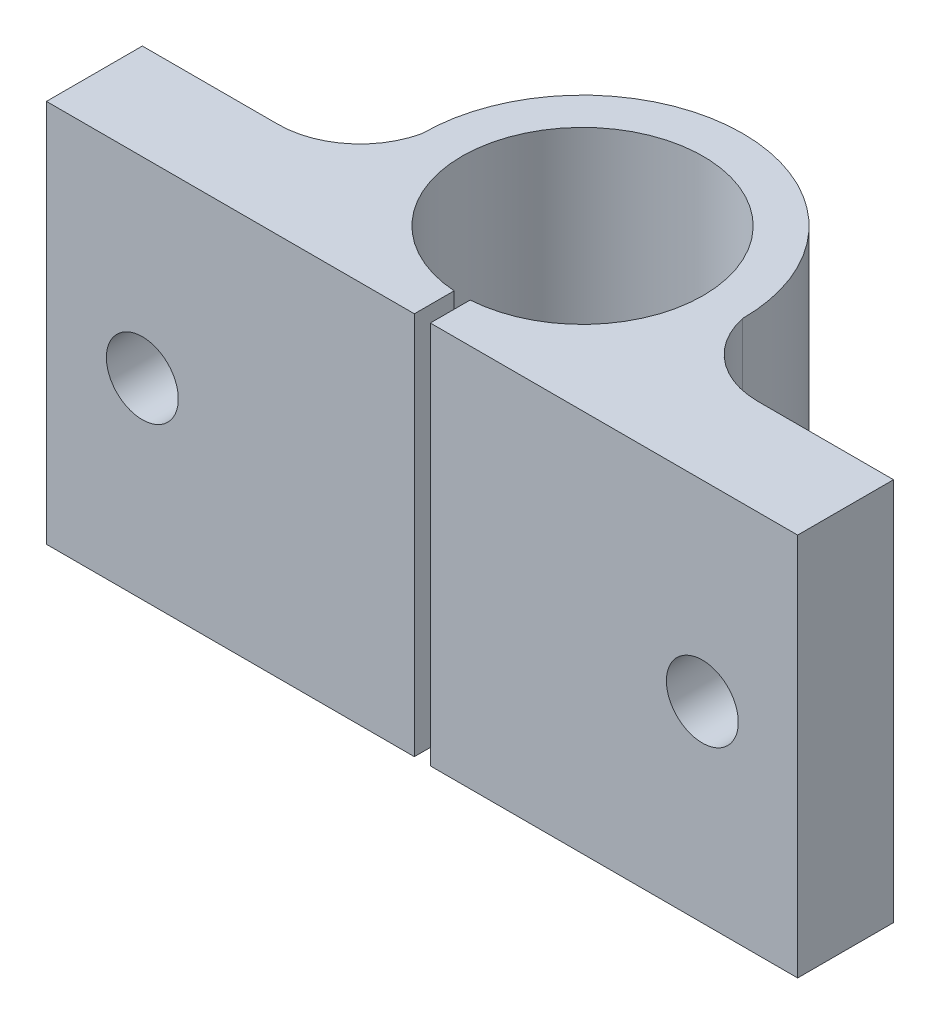
SolidWorks part; units mm, degrees
ref_plane "Front Plane" through (0, 0, 0) normal (0, 0, 1) x (1, 0, 0)
ref_plane "Top Plane" through (0, 0, 0) normal (0, 1, 0) x (1, 0, 0)
ref_plane "Right Plane" through (0, 0, 0) normal (1, 0, 0) x (0, 0, -1)
ref_plane "Plane1" through (0, 24, 0) normal (0, 1, 0) x (1, 0, 0)
sketch "Sketch1" plane through (0, 24, 0) normal (0, 1, 0) x (1, 0, 0)
  line L0 (0, 0) -> (47, 0)
  line L1 (47, 0) -> (47, 6)
  line L2 (47, 6) -> (38.5, 6)
  line L3 (8.5, 6) -> (0, 6)
  line L4 (0, 6) -> (0, 0)
  arc A0 (38.5, 6) -> (33.5414, 10.0218) centre (38.5, 11.0678) cw
  arc A1 (33.5414, 10.0218) -> (13.4959, 9.9961) centre (23.5186, 10.0227) ccw
  arc A2 (13.4959, 9.9961) -> (8.5, 6) centre (8.5, 11.121) cw
extrude "Boss-Extrude1" add sketch "Sketch1" against normal blind 24
sketch "Sketch2" plane through (0, 0, 0) normal (0, -1, 0) x (1, 0, 0)
  line L0 (24.0186, 0) -> (23.0186, 0)
  line L1 (23.0186, 0) -> (23.0186, -2.4893)
  line L2 (24.0186, -2.4893) -> (24.0186, 0)
  arc A0 (23.0186, -2.4893) -> (24.0186, -2.4893) centre (23.5186, -10.0227) cw
extrude "Cut-Extrude1" cut sketch "Sketch2" against normal through all
ref_plane "Plane2" through (0, 0, -10.0227) normal (0, 0, -1) x (-1, 0, 0)
sketch "Sketch3" plane through (0, 0, -10.0227) normal (0, 0, -1) x (-1, 0, 0)
  line L0 (-31.0686, 0) -> (-23.5186, 0)
  line L1 (-23.5186, 0) -> (-23.5186, 24)
  line L2 (-23.5186, 24) -> (-31.0686, 24)
  line L3 (-31.0686, 24) -> (-31.0686, 0)
  line L4 (-23.5186, 0) -> (-23.5186, 24) construction
revolve "Cut-Revolve1" cut sketch "Sketch3" angle 360 about L4
hole_wizard "Ø4.5 (4.5) Diameter Hole1" positions "Sketch5" profile "Sketch4" hole size "Ø4.5" standard "ANSI Metric"
sketch "Sketch5" plane through (0, 0, -6) normal (0, 0, -1) x (-1, 0, 0)
  point P0 (-41.0373, 12)
  point P1 (-6, 12)
sketch "Sketch4" plane through (41.0373, 12, -6) normal (1, 0, 0) x (0, 1, 0)
  line L0 (0, 0) -> (0, 6)
  line L1 (0, 6) -> (2.25, 6)
  line L2 (2.25, 6) -> (2.25, 0)
  line L5 (2.25, 0) -> (0, 0)
  line L11 (0, -6.35) -> (0, 107.95) construction
  dimension "Thru Hole Dia." = 4.5
  dimension "Thru Hole Depth" = 6
